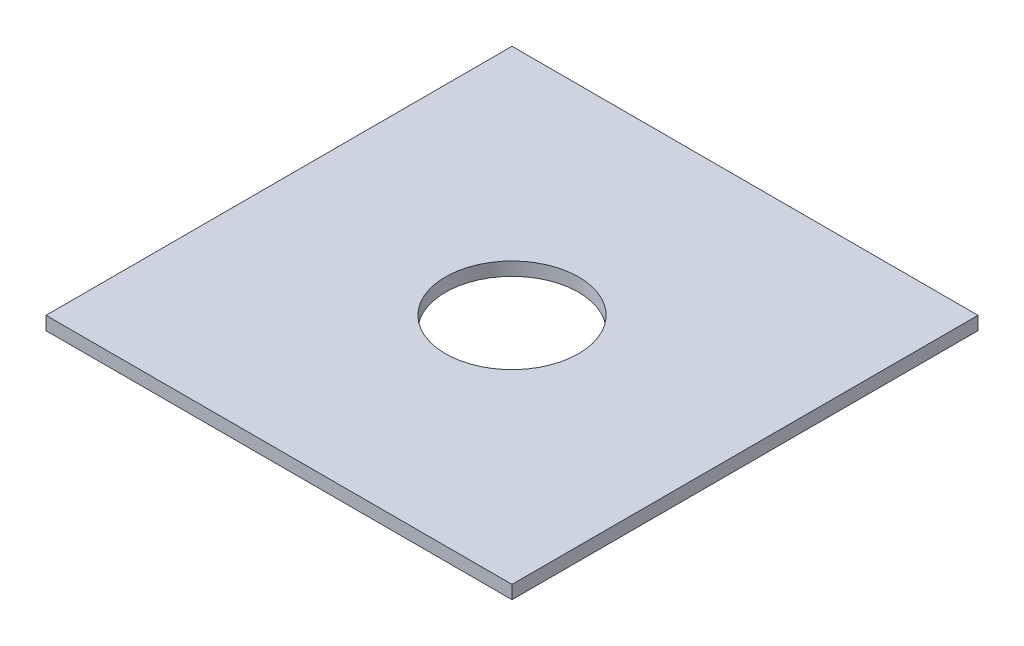
SolidWorks part; units mm, degrees
ref_plane "Face" through (0, 0, 0) normal (0, 0, 1) x (1, 0, 0)
ref_plane "Dessus" through (0, 0, 0) normal (0, 1, 0) x (1, 0, 0)
ref_plane "Droite" through (0, 0, 0) normal (1, 0, 0) x (0, 0, -1)
sketch "Esquisse1" plane through (0, 0, 0) normal (0, 1, 0) x (1, 0, 0)
  line L1 (0, 0) -> (350, 0)
  line L2 (0, 0) -> (0, 350)
  line L3 (0, 350) -> (350, 350)
  line L4 (350, 0) -> (350, 350)
  dimension "D1" = 350
  dimension "D2" = 350
extrude "Extrusion1" add sketch "Esquisse1" along normal blind 10
sketch "Esquisse2" plane through (0, 10, 0) normal (0, 1, 0) x (1, 0, 0)
  line L0 (175, 0) -> (175, 350)
  line L1 (0, 0) -> (350, 0) construction
  line L2 (350, 350) -> (0, 350) construction
  line L3 (0, 175) -> (350, 175)
  line L4 (0, 350) -> (0, 0) construction
  line L5 (350, 0) -> (350, 350) construction
  circle A0 centre (175, 175) radius 50
  dimension "D1" = 100
extrude "Extrusion2" cut sketch "Esquisse2" against normal blind 10 contours A0
